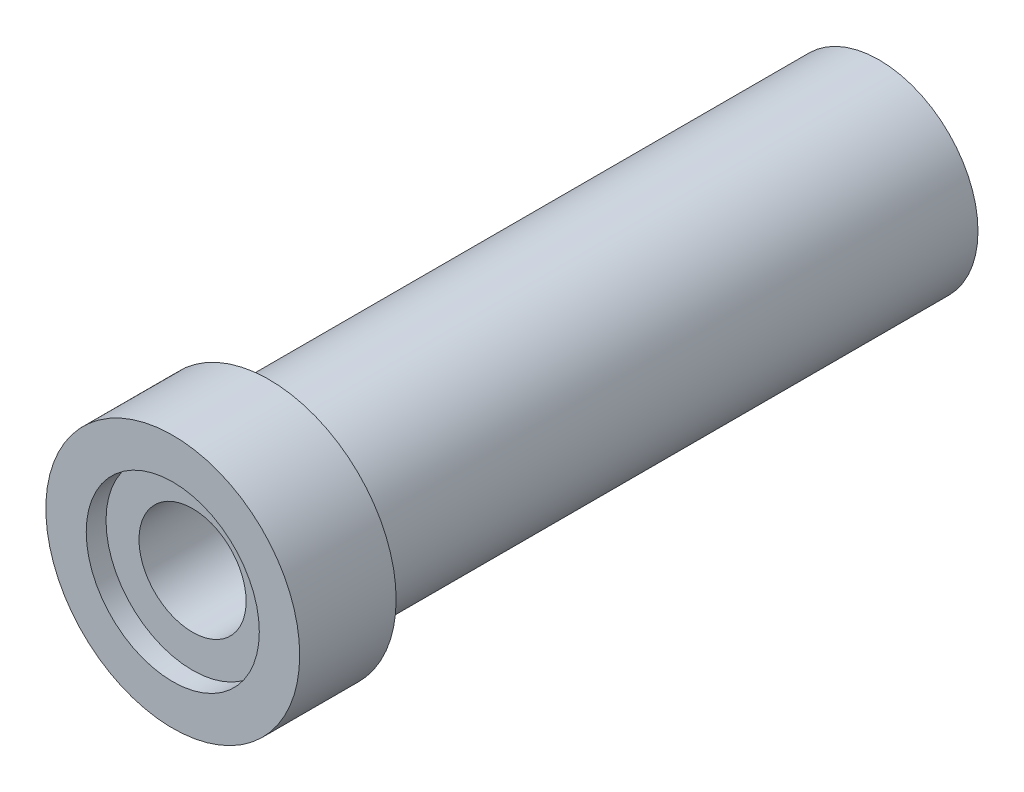
SolidWorks part; units mm, degrees
material "ABS PC"
ref_plane "Front Plane" through (0, 0, 0) normal (0, 0, 1) x (1, 0, 0)
ref_plane "Top Plane" through (0, 0, 0) normal (0, 1, 0) x (1, 0, 0)
ref_plane "Right Plane" through (0, 0, 0) normal (1, 0, 0) x (0, 0, -1)
sketch "Sketch1" plane through (0, 0, 0) normal (0, 0, 1) x (1, 0, 0)
  circle A0 centre (0, 0) radius 7.7
  circle A1 centre (0, 0) radius 3.25
  dimension "D1" = 15.4
  dimension "D2" = 6.5
extrude "Boss-Extrude1" add sketch "Sketch1" along normal blind 5.85
sketch "Sketch2" plane through (0, 0, 5.85) normal (0, 0, 1) x (1, 0, 0)
  circle A0 centre (0, 0) radius 5.25
extrude "Cut-Extrude1" cut sketch "Sketch2" against normal blind 1.2
sketch "Sketch4" plane through (0, 0, 0) normal (0, 0, -1) x (-1, 0, 0)
  circle A0 centre (0, 0) radius 3.25
  circle A1 centre (0, 0) radius 6
  dimension "D1" = 6.5
  dimension "D2" = 12
extrude "Boss-Extrude2" add sketch "Sketch4" along normal blind 7
sketch "Sketch5" plane through (0, 0, -7) normal (0, 0, -1) x (-1, 0, 0)
  circle A0 centre (0, 0) radius 4.6
  circle A1 centre (0, 0) radius 6
  circle A2 centre (0, 0) radius 3.25
  circle M1 centre (0, 0) radius 6
extrude "Boss-Extrude5" add sketch "Sketch5" along normal blind 30 contours A0 M1
